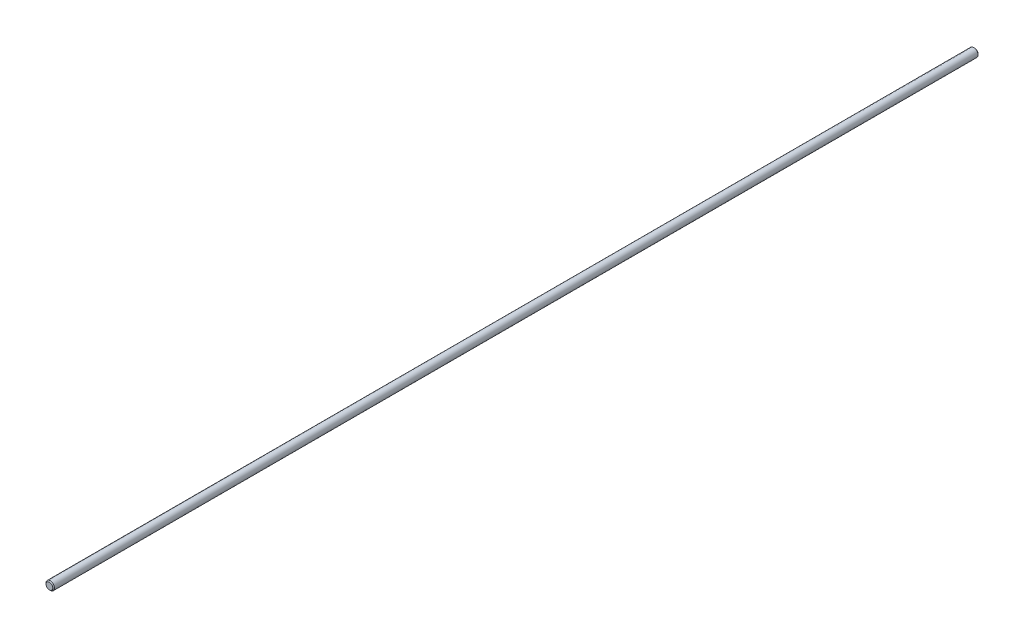
SolidWorks part; units mm, degrees
material "Chrome Stainless Steel"
ref_plane "Front Plane" through (0, 0, 0) normal (0, 0, 1) x (1, 0, 0)
ref_plane "Top Plane" through (0, 0, 0) normal (0, 1, 0) x (1, 0, 0)
ref_plane "Right Plane" through (0, 0, 0) normal (1, 0, 0) x (0, 0, -1)
sketch "Sketch1" plane through (0, 0, 0) normal (0, 0, 1) x (1, 0, 0)
  circle A0 centre (0, 0) radius 5
  dimension "D1" = 10
extrude "Boss-Extrude1" add sketch "Sketch1" along normal blind 1093
chamfer "Chamfer1" distance 1 angle 45 2 edges at (5, 0, 0) (5, 0, 1093)
